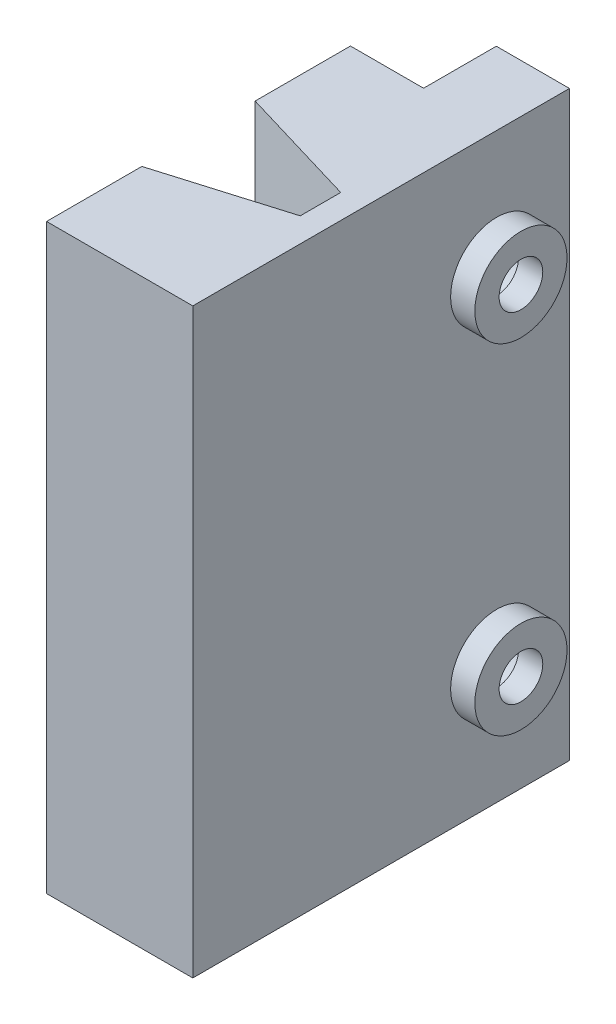
SolidWorks part; units mm, degrees
ref_plane "Front Plane" through (0, 0, 0) normal (0, 0, 1) x (1, 0, 0)
ref_plane "Top Plane" through (0, 0, 0) normal (0, 1, 0) x (1, 0, 0)
ref_plane "Right Plane" through (0, 0, 0) normal (1, 0, 0) x (0, 0, -1)
sketch "Sketch1" plane through (0, 0, 0) normal (0, 1, 0) x (1, 0, 0)
  line L0 (0.7588, 5.315) -> (5, 5.315)
  line L1 (-1.03, 5.315) -> (0.7588, 5.315)
  line L2 (-1.03, 5.315) -> (-1.03, -0.115)
  line L3 (-1.03, -7.215) -> (1.3982, -7.215)
  line L15 (-1.03, -0.115) -> (4, -0.115)
  line L17 (-1.03, -1.785) -> (4, -1.785)
  line L18 (4, -0.115) -> (4, -1.785)
  line L21 (5, 5.315) -> (5, -7.215)
  line L22 (5, -7.215) -> (1.3982, -7.215)
  line L23 (-1.03, -1.785) -> (-1.03, -7.215)
  point P0 (0, 0)
  dimension "D12" = 1
extrude "Boss-Extrude1" add sketch "Sketch1" along normal blind 24
ref_plane "Plane2" through (0, 0, 0.95) normal (0, 0, 1) x (1, 0, 0)
sketch "Sketch7" plane through (0, 0, -5.315) normal (0, 0, -1) x (-1, 0, 0)
  line L0 (-5, 0) -> (1.03, 0) construction
  line L1 (-5, 24) -> (-1.985, 24)
  line L2 (-5, 24) -> (-5, 0)
  line L3 (-5, 0) -> (-1.985, 0)
  line L4 (-1.985, 24) -> (-1.985, 0)
extrude "Boss-Extrude3" add sketch "Sketch7" along normal blind 3
sketch "Sketch3" plane through (5, 0, 0) normal (1, 0, 0) x (0, 0, -1)
  line L1 (8.315, 24) -> (8.315, 0) construction
  line L2 (-7.215, 0) -> (8.315, 0) construction
  line L3 (-7.215, 24) -> (8.315, 24) construction
  circle A0 centre (5.315, 19) radius 0.9
  circle A1 centre (5.315, 5) radius 0.9
  circle A2 centre (5.315, 19) radius 1.9
  circle A3 centre (5.315, 5) radius 1.9
  dimension "D1" = 1.8
  dimension "D2" = 1.8
  dimension "D5" = 5
  dimension "D6" = 5
  dimension "D7" = 1
  dimension "D8" = 1
  dimension "D3" = 3
  dimension "D4" = 3
extrude "Boss-Extrude2" add sketch "Sketch3" along normal blind 1
sketch "Sketch4" plane through (5, 0, 0) normal (1, 0, 0) x (0, 0, -1)
  circle A0 centre (5.315, 19) radius 1.15
  circle A1 centre (5.315, 5) radius 1.15
extrude "Cut-Extrude2" cut sketch "Sketch4" against normal blind 23
sketch "Sketch6" plane through (0, 24, 0) normal (0, 1, 0) x (1, 0, 0)
  line L0 (4, -0.115) -> (-1.03, 1.385)
  line L1 (-1.03, 5.315) -> (-1.03, -0.115) construction
  line L2 (-1.03, 1.385) -> (-1.03, -0.115)
  line L3 (-1.03, -0.115) -> (4, -0.115)
  line L4 (-1.03, -1.785) -> (4, -1.785)
  line L5 (4, -1.785) -> (-1.03, -3.285)
  line L6 (-1.03, -1.785) -> (-1.03, -7.215) construction
  line M4 (-1.03, 5.315) -> (-1.03, -0.115)
  line M5 (-1.03, -0.115) -> (4, -0.115)
  line M7 (4, -1.785) -> (-1.03, -1.785)
  line M8 (-1.03, -1.785) -> (-1.03, -7.215)
  dimension "D1" = 1.5
  dimension "D2" = 1.5
extrude "Cut-Extrude3" cut sketch "Sketch6" against normal blind 30 contours L0 M5 M4 | L5 M7 M8
